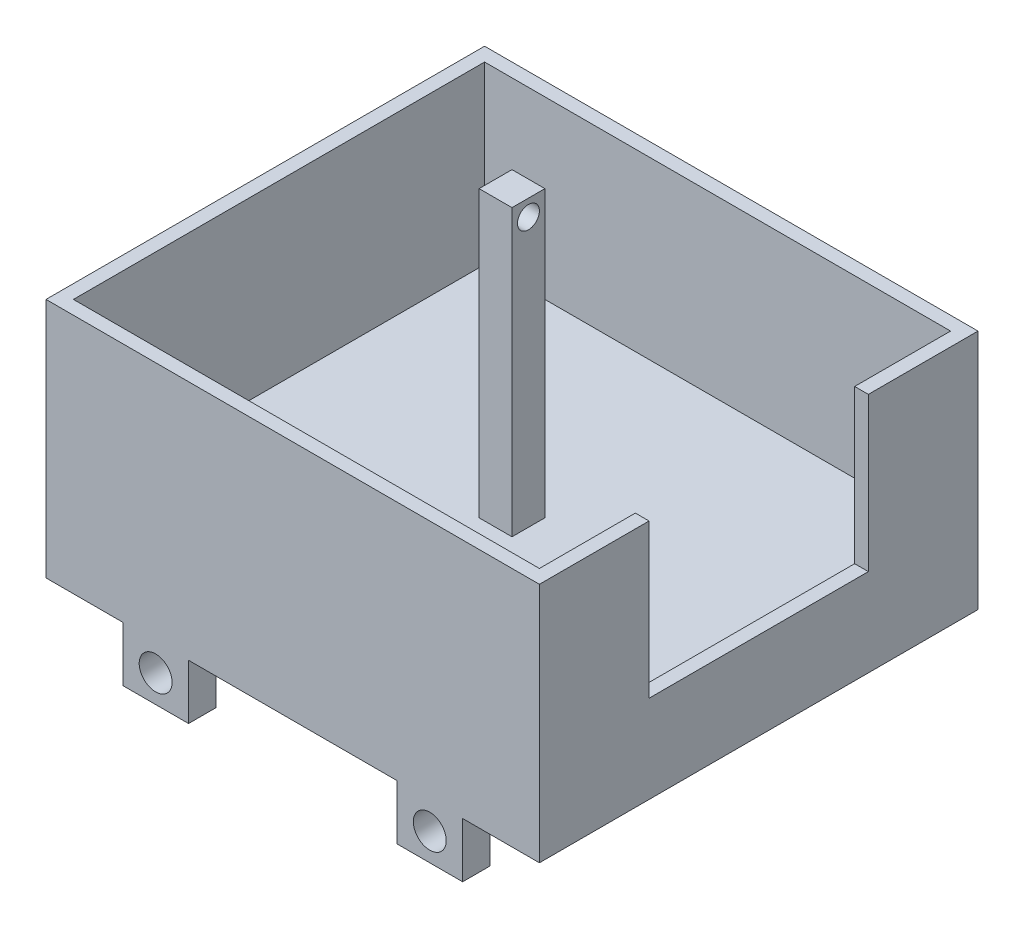
SolidWorks part; units mm, degrees
ref_plane "Front Plane" through (0, 0, 0) normal (0, 0, 1) x (1, 0, 0)
ref_plane "Top Plane" through (0, 0, 0) normal (0, 1, 0) x (1, 0, 0)
ref_plane "Right Plane" through (0, 0, 0) normal (1, 0, 0) x (0, 0, -1)
sketch "Sketch1" plane through (0, 0, 0) normal (0, 1, 0) x (1, 0, 0)
  line L1 (-225, 200) -> (225, 200)
  line L2 (-225, 200) -> (-225, -200)
  line L3 (-225, -200) -> (225, -200)
  line L4 (225, 200) -> (225, -200)
  line L5 (-225, 200) -> (225, -200) construction
  line L6 (-225, -200) -> (225, 200) construction
  point P0 (0, 0)
  dimension "D1" = 450
  dimension "D2" = 400
extrude "Boss-Extrude1" add sketch "Sketch1" along normal blind 220
sketch "Sketch2" plane through (0, 220, 0) normal (0, 1, 0) x (1, 0, 0)
  line L1 (-212.5, 187.5) -> (212.5, 187.5)
  line L2 (-212.5, 187.5) -> (-212.5, -187.5)
  line L3 (-212.5, -187.5) -> (212.5, -187.5)
  line L4 (212.5, 187.5) -> (212.5, -187.5)
  line L5 (-212.5, 187.5) -> (212.5, -187.5) construction
  line L6 (-212.5, -187.5) -> (212.5, 187.5) construction
  point P0 (0, 0)
  dimension "D1" = 425
  dimension "D2" = 375
extrude "Cut-Extrude1" cut sketch "Sketch2" against normal blind 160
sketch "Sketch3" plane through (225, 0, 0) normal (1, 0, 0) x (0, 0, -1)
  line L0 (-200, 220) -> (200, 220) construction
  line L1 (-100, 220) -> (100, 220)
  line L2 (-100, 220) -> (-100, 80)
  line L3 (-100, 80) -> (100, 80)
  line L4 (100, 220) -> (100, 80)
  line L5 (200, 220) -> (200, 0) construction
  dimension "D1" = 140
  dimension "D2" = 200
  dimension "D3" = 100
extrude "Cut-Extrude2" cut sketch "Sketch3" against normal blind 12.5 contours L2 L1 L4 L3
sketch "Sketch4" plane through (0, 60, 0) normal (0, 1, 0) x (1, 0, 0)
  line L1 (-15, 15) -> (15, 15)
  line L2 (-15, 15) -> (-15, -15)
  line L3 (-15, -15) -> (15, -15)
  line L4 (15, 15) -> (15, -15)
  line L5 (-15, 15) -> (15, -15) construction
  line L6 (-15, -15) -> (15, 15) construction
  point P0 (0, 0)
  dimension "D1" = 30
  dimension "D2" = 30
extrude "Boss-Extrude2" add sketch "Sketch4" along normal blind 260
sketch "Sketch5" plane through (15, 0, 0) normal (1, 0, 0) x (0, 0, -1)
  line L0 (-15, 320) -> (15, 320) construction
  line L2 (15, 320) -> (15, 60) construction
  circle A0 centre (0, 305) radius 10
  dimension "D2" = 20
  dimension "D1" = 15
  dimension "D3" = 15
extrude "Cut-Extrude3" cut sketch "Sketch5" against normal blind 30
sketch "Sketch6" plane through (0, 0, 0) normal (0, -1, 0) x (1, 0, 0)
  line L0 (-225, 200) -> (225, 200) construction
  line L1 (95, 200) -> (155, 200)
  line L2 (95, 200) -> (95, 175)
  line L3 (95, 175) -> (155, 175)
  line L4 (155, 200) -> (155, 175)
  line L5 (225, 200) -> (225, -200) construction
  line L6 (-155, 175) -> (-95, 175)
  line L7 (-95, 200) -> (-95, 175)
  line L8 (-155, 200) -> (-95, 200)
  line L9 (-155, 200) -> (-155, 175)
  line L10 (-155, -200) -> (-95, -200)
  line L11 (-95, -175) -> (-95, -200)
  line L12 (-155, -175) -> (-95, -175)
  line L13 (-155, -175) -> (-155, -200)
  line L14 (95, -200) -> (155, -200)
  line L15 (155, -175) -> (155, -200)
  line L16 (95, -175) -> (155, -175)
  line L17 (95, -175) -> (95, -200)
  line L18 (-225, -200) -> (-225, 200) construction
  point P6 (155, 187.5)
  point P9 (155, -187.5)
  dimension "D1" = 60
  dimension "D2" = 25
  dimension "D3" = 70
  dimension "D6" = 70
  dimension "D7" = 70
  dimension "D8" = 350
  dimension "D4" = 2
  dimension "D5" = 2
extrude "Boss-Extrude3" add sketch "Sketch6" along normal blind 50
sketch "Sketch7" plane through (0, 0, -200) normal (0, 0, -1) x (-1, 0, 0)
  line L0 (155, -50) -> (155, 0) construction
  line L1 (155, -50) -> (95, -50) construction
  line L2 (-155, -50) -> (-155, 0) construction
  line L3 (-95, -50) -> (-155, -50) construction
  circle A0 centre (125, -25) radius 15
  circle A1 centre (-125, -25) radius 15
  dimension "D1" = 30
  dimension "D4" = 30
  dimension "D2" = 30
  dimension "D3" = 25
  dimension "D5" = 30
  dimension "D6" = 25
extrude "Cut-Extrude4" cut sketch "Sketch7" against normal up to surface (25 mm away) up to face at (-125, -25, -175)
sketch "Sketch8" plane through (0, 0, 200) normal (0, 0, 1) x (1, 0, 0)
  line L0 (155, -50) -> (155, 0) construction
  line L1 (155, -50) -> (95, -50) construction
  line L2 (-95, -50) -> (-95, 0) construction
  line L3 (-95, -50) -> (-155, -50) construction
  circle A0 centre (-125, -25) radius 15
  circle A1 centre (125, -25) radius 15
  dimension "D1" = 30
  dimension "D2" = 30
  dimension "D3" = 30
  dimension "D4" = 25
  dimension "D5" = 30
  dimension "D6" = 25
extrude "Cut-Extrude5" cut sketch "Sketch8" against normal up to surface (25 mm away) up to face at (125, -25, 175)
